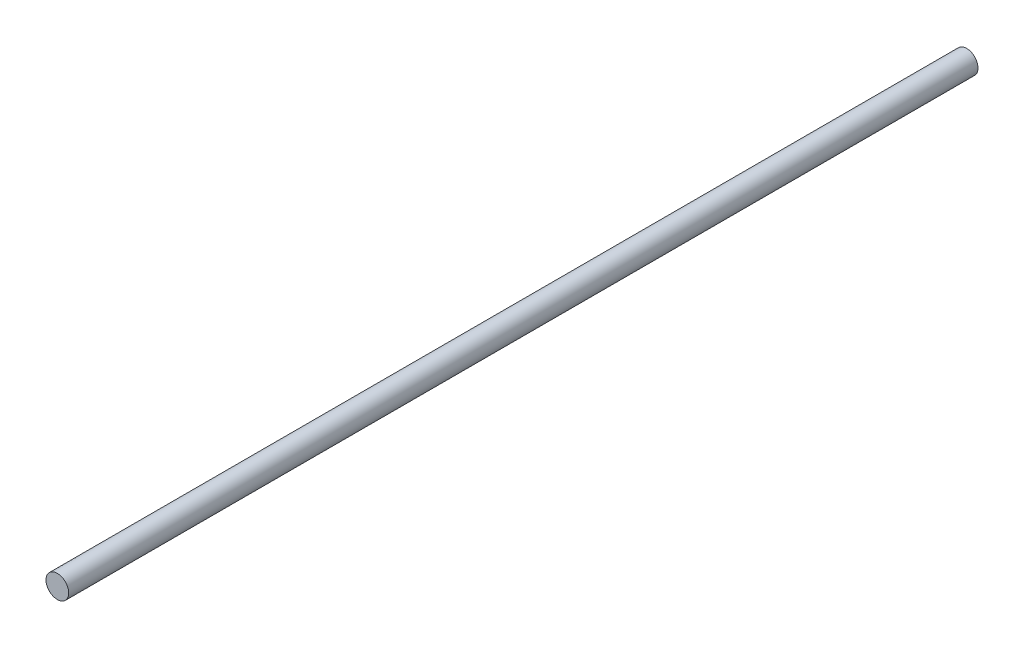
SolidWorks part; units mm, degrees
ref_plane "Front" through (0, 0, 0) normal (0, 0, 1) x (1, 0, 0)
ref_plane "Top" through (0, 0, 0) normal (0, 1, 0) x (1, 0, 0)
ref_plane "Right" through (0, 0, 0) normal (1, 0, 0) x (0, 0, -1)
sketch "Sketch1" plane through (0, 0, 0) normal (0, 0, 1) x (1, 0, 0)
  circle A0 centre (0, 0) radius 3.175
extrude "Boss-Extrude1" add sketch "Sketch1" along normal blind 254
